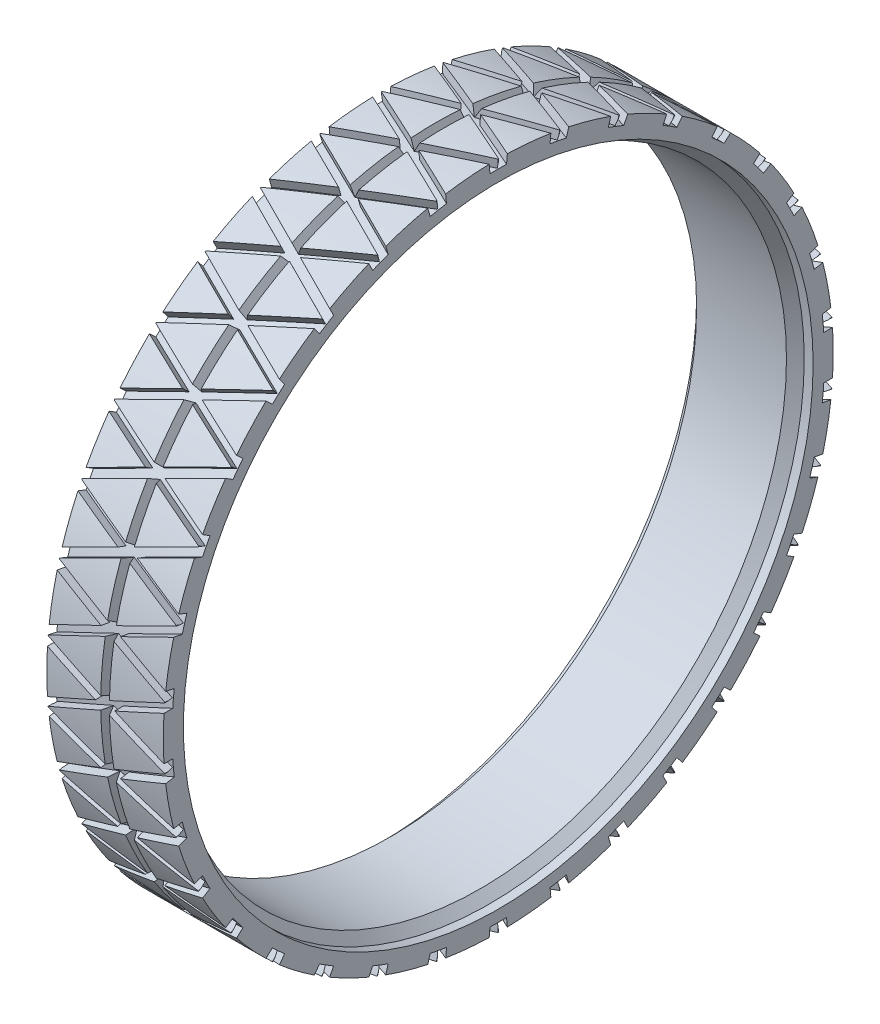
SolidWorks part; units mm, degrees
ref_plane "Front Plane" through (0, 0, 0) normal (0, 0, 1) x (1, 0, 0)
ref_plane "Top Plane" through (0, 0, 0) normal (0, 1, 0) x (1, 0, 0)
ref_plane "Right Plane" through (0, 0, 0) normal (1, 0, 0) x (0, 0, -1)
sketch "Sketch1" plane through (0, 0, 0) normal (0, 0, 1) x (1, 0, 0)
  line L0 (-20, 115) -> (20, 115)
  line L1 (-20, 115) -> (-20, 108.1)
  line L2 (-20, 108.1) -> (-16.95, 108.1)
  line L3 (-16.95, 108.1) -> (-16.95, 105.05)
  line L4 (-16.95, 105.05) -> (13.9, 105.05)
  line L5 (13.9, 105.05) -> (16.95, 108.1)
  line L6 (16.95, 108.1) -> (20, 108.1)
  line L7 (20, 108.1) -> (20, 115)
  point P2 (0, 115)
  dimension "D2" = 3.05
  dimension "D1" = 20
  dimension "D3" = 3.05
  dimension "D4" = 3.05
  dimension "D5" = 3.05
  dimension "D6" = 115
  dimension "D7" = 3.05
  dimension "D8" = 105.05
ref_axis "Axis1" through (22, 0, 0) along (-1, 0, 0)
revolve "Revolve1" add sketch "Sketch1" angle 360 about axis through (22, 0, 0) along (-1, 0, 0)
sketch "Sketch2" plane through (0, 0, 0) normal (0, 0, 1) x (1, 0, 0)
  line L0 (-20, 112) -> (20, 112)
  dimension "D1" = 112
surface "Surface-Revolve1" sketch "Sketch2" parameters "D1"=360
ref_plane "Plane1" through (0, 0, 117) normal (0, 0, 1) x (1, 0, 0)
sketch "Sketch3" plane through (0, 0, 117) normal (0, 0, 1) x (1, 0, 0)
  line L0 (-20, 7.5) -> (-3.3333, 0)
  line L1 (-20, -112) -> (-20, 112) construction
  line L2 (20, -115) -> (20, 115) construction
  line L3 (20, -10.5) -> (20, -7.5)
  line L4 (20, -7.5) -> (3.3333, 0)
  line L5 (-20, 10.5) -> (-20, 7.5)
  line L6 (20, 7.5) -> (3.3333, 0)
  line L7 (-20, -10.5) -> (-20, -7.5)
  line L8 (-20, 115) -> (-20, -115) construction
  line L9 (-20, -7.5) -> (-3.3333, 0)
  line L10 (20, 10.5) -> (20, 7.5)
  line L11 (0, 1.5) -> (-20, 10.5)
  line L12 (0, -1.5) -> (20, -10.5)
  line L13 (0, 1.5) -> (20, 10.5)
  line L14 (0, -1.5) -> (-20, -10.5)
  dimension "D1" = 3
  dimension "D2" = 3
  dimension "D3" = 15
  dimension "D4" = 15
  dimension "D5" = 7.5
extrude "Cut-Extrude1" cut sketch "Sketch3" against normal up to surface (5.01 mm away)
pattern_circular "CirPattern1" count 34 over 360 about axis through (0, 0, 0) along (1, 0, 0) of "Cut-Extrude1"
sketch "Sketch4" plane through (0, 0, 0) normal (0, 0, 1) x (1, 0, 0)
  line L0 (20, 115) -> (-20, 115) construction
  line L3 (-1.5, 115) -> (1.5, 115)
  line L5 (-0.5, 113) -> (1.5, 115) construction
  line L6 (-1.5, 115) -> (0.5, 113) construction
  line L7 (-1.5, 115) -> (0, 112)
  line L8 (0, 112) -> (1.5, 115)
  point P0 (0, 113.5)
  dimension "D1" = 115
  dimension "D2" = 3
  dimension "D3" = 3
  dimension "D4" = 1.5
revolve "Cut-Revolve1" cut sketch "Sketch4" angle 360 about axis through (22, 0, 0) along (-1, 0, 0)
delete or keep bodies "Body-Delete/Keep 1" type delete bodies bodies 102
